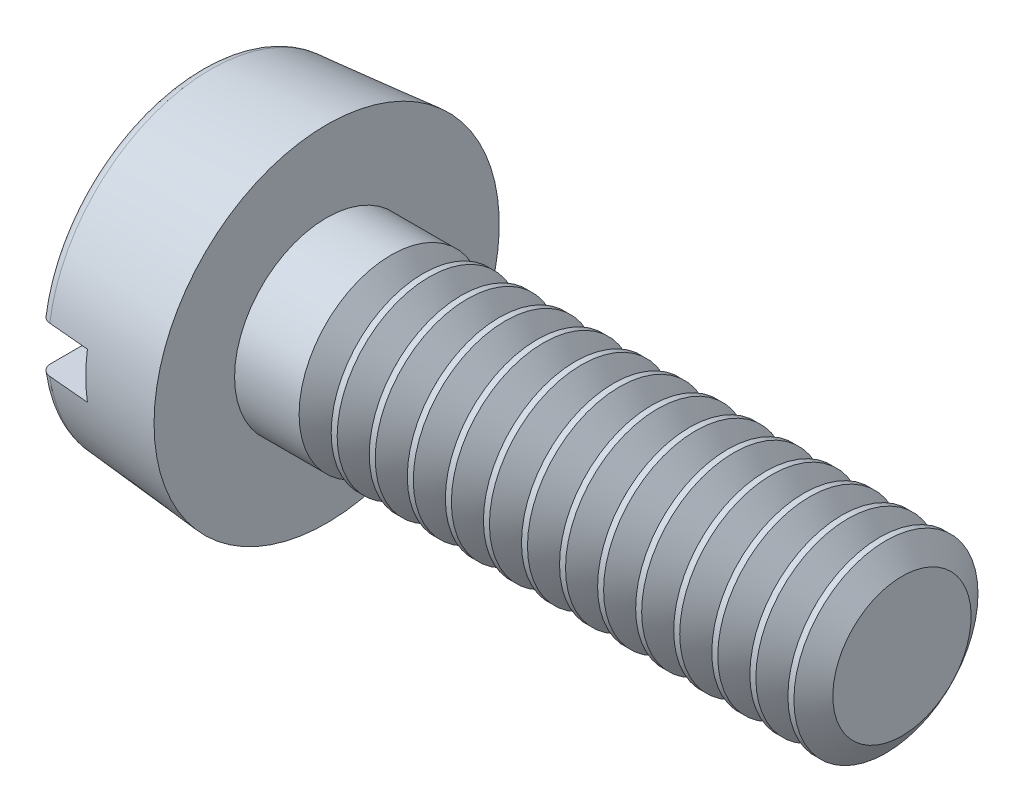
SolidWorks part; units mm, degrees
ref_plane "Plane1" through (0, 0, 0) normal (0, 0, 1) x (1, 0, 0)
ref_plane "Plane2" through (0, 0, 0) normal (0, 1, 0) x (1, 0, 0)
ref_plane "Plane3" through (0, 0, 0) normal (1, 0, 0) x (0, 0, -1)
sketch "BodySke" plane through (0, 0, 0) normal (0, 0, 1) x (1, 0, 0)
  line L0 (1.1, 0.8) -> (1.1, 1.5)
  line L1 (0, 0) -> (0, 1.4038)
  line L2 (-25.4, 0) -> (127, 0) construction
  line L3 (6.1, 0) -> (0, 0)
  line L4 (1.1, 0.8) -> (6.1, 0.8)
  line L5 (6.1, 0.8) -> (6.1, 0)
  line L6 (0, 1.4038) -> (1.1, 1.5)
  line L9 (1.45, 2.3875) -> (1.45, -7.1375) construction
  line L10 (1.1, 6.35) -> (1.1, -3.175) construction
  dimension "Head_ht" = 1.1
  dimension "Diameter" = 1.6
  dimension "Length" = 5
  dimension "Head_dia" = 3
  dimension "Advance" = 0.35
  dimension "Thread_nom" = 5
  dimension "Head_side_angle" = 5
revolve "Base-Revolve" add sketch "BodySke"
cosmetic thread "ThreadCosmetic" [suppressed]
fillet "Fillet1" [suppressed] radius 0.1
fillet "Fillet2" radius 0.1 1 edges at (0, 0, 1.4038)
sketch "Sketch2" plane through (0, 0, 0) normal (1, 0, 0) x (0, 0, -1)
  line L0 (1.5, -0.2) -> (-1.5, -0.2)
  line L1 (1.5, -0.2) -> (1.5, 0.2)
  line L2 (-1.5, 0.2) -> (1.5, 0.2)
  line L3 (-1.5, 0.2) -> (-1.5, -0.2)
  dimension "D1" = 3
  dimension "D2" = 1.5
  dimension "Slot_width" = 0.4
  dimension "D3" = 0.2
extrude "Slot" cut sketch "Sketch2" along normal blind 0.45
sketch "ThdSchSke" plane through (0, 0, 0) normal (0, 0, 1) x (1, 0, 0)
  line L0 (1.8, -0.601) -> (1.6607, -0.8)
  line L1 (1.8, -0.601) -> (1.9393, -0.8)
  line L2 (1.9393, -0.8) -> (1.9393, -1)
  line L3 (-3.175, 0) -> (5.1513, 0) construction
  line L5 (1.9393, -1) -> (1.6607, -1)
  line L6 (1.6607, -1) -> (1.6607, -0.8)
  dimension "Thread_minor" = 1.202
  dimension "Diameter" = 1.6
  dimension "Start" = 1.8
  dimension "SideAngle" = 55
  dimension "VeeAngle" = 70
  dimension "Overcut" = 2
revolve "ThreadSchematic" cut sketch "ThdSchSke" angle 360 about L3
pattern_linear "ThdSchPat" count 14 spacing 0.3308 along (1, 0, 0) of "ThreadSchematic"
equation "\"D1@Sketch2\" = \"Head_dia@BodySke\""
equation "\"D2@Sketch2\" = \"D1@Sketch2\" / 2"
equation "\"D3@Sketch2\" = \"Slot_width@Sketch2\" / 2"
equation "\"Thread_length@ThreadCosmetic\" = ((sgn( (\"Length@BodySke\" - \"Advance@BodySke\" * 2.0 ) - \"Thread_nom@BodySke\" )-1)*( (\"Length@BodySke\" - \"Advance@BodySke\"  * 2.0) - \"Thread_nom@BodySke\" ))/-2+ \"Thread_nom@BodySke\""
equation "\"Thread_minor@ThdSchSke\" = \"Thread_minor@ThreadCosmetic\""
equation "\"Diameter@ThdSchSke\" = \"Diameter@BodySke\""
equation "\"Overcut@ThdSchSke\" = \"Diameter@BodySke\" * 1.25"
equation "\"Start@ThdSchSke\" = \"Head_ht@BodySke\" + \"Length@BodySke\" - \"Thread_length@ThreadCosmetic\"  '---Non-countersunk---"
equation "\"Num_threads@ThdSchPat\" = int( \"Thread_length@ThreadCosmetic\" / \"Advance@BodySke\" + 0.999 )  + 1"
equation "\"Advance@ThdSchPat\" = \"Thread_length@ThreadCosmetic\" /  (\"Num_threads@ThdSchPat\" - 1) 'relax it"
